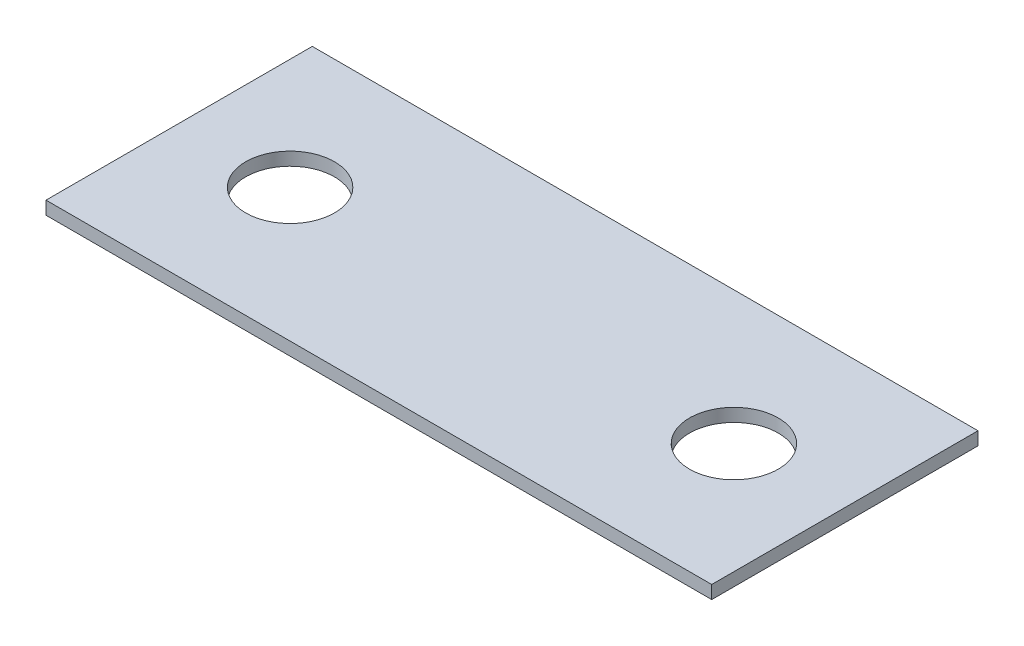
SolidWorks part; units mm, degrees
ref_plane "Front Plane" through (0, 0, 0) normal (0, 0, 1) x (1, 0, 0)
ref_plane "Top Plane" through (0, 0, 0) normal (0, 1, 0) x (1, 0, 0)
ref_plane "Right Plane" through (0, 0, 0) normal (1, 0, 0) x (0, 0, -1)
sketch "Sketch1" plane through (0, 0, 0) normal (0, 1, 0) x (1, 0, 0)
  line L1 (0, 0) -> (47.625, 0)
  line L2 (0, 0) -> (0, -19.05)
  line L3 (0, -19.05) -> (47.625, -19.05)
  line L4 (47.625, 0) -> (47.625, -19.05)
  dimension "D1" = 47.625
  dimension "D2" = 19.05
extrude "Boss-Extrude1" add sketch "Sketch1" along normal blind 0.9375
sketch "Sketch2" plane through (0, 0.9375, 0) normal (0, 1, 0) x (1, 0, 0)
  line L0 (0, 0) -> (0, -19.05) construction
  line L1 (7.9375, -9.525) -> (39.6875, -9.525) construction
  line L3 (47.625, 0) -> (0, 0) construction
  circle A0 centre (7.9375, -9.525) radius 3.175
  circle A1 centre (39.6875, -9.525) radius 3.175
  point P4 (23.8125, -9.525)
  point P8 (0, -9.525)
  point P10 (23.8125, 0)
  dimension "D1" = 31.75
  dimension "D2" = 6.35
extrude "Cut-Extrude1" cut sketch "Sketch2" against normal up to next
